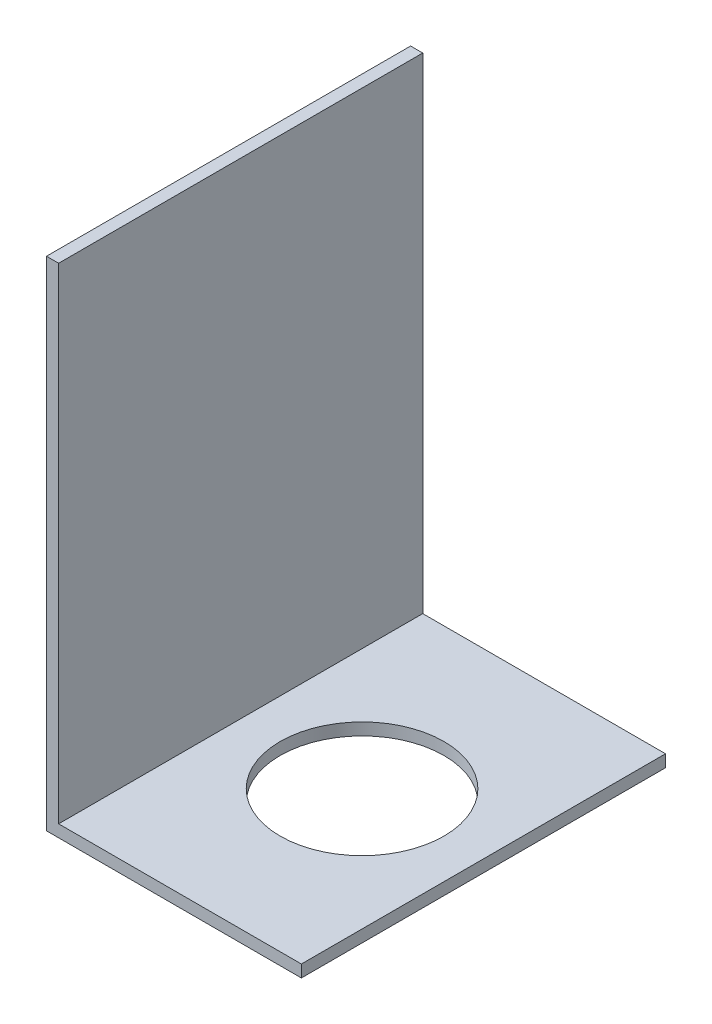
SolidWorks part; units mm, degrees
ref_plane "Front Plane" through (0, 0, 0) normal (0, 0, 1) x (1, 0, 0)
ref_plane "Top Plane" through (0, 0, 0) normal (0, 1, 0) x (1, 0, 0)
ref_plane "Right Plane" through (0, 0, 0) normal (1, 0, 0) x (0, 0, -1)
sketch "Sketch1" plane through (0, 0, 0) normal (0, 0, 1) x (1, 0, 0)
  line L0 (0, 40) -> (0, 0)
  line L1 (0, 0) -> (20, 0)
  dimension "D1" = 40
  dimension "D2" = 20
extrude "Extrude-Thin1" add sketch "Sketch1" along normal mid plane 30 thin
hole_wizard "M12 Clearance Slot1" positions "Sketch5" profile "Sketch4" size "M12" standard "ISO" slot yes end condition up to next
sketch "Sketch5" plane through (0, 0, 0) normal (0, 1, 0) x (1, 0, 0)
  line L0 (0, 15) -> (20, 15) construction
  line L2 (0, -15) -> (0, 15) construction
  point P0 (10, 0)
  dimension "D1" = 15
  dimension "D2" = 10
sketch "Sketch4" plane through (10, 0, 0) normal (1, 0, 0) x (0, 0, 1)
  line L0 (0, 0) -> (0, 1)
  line L1 (0, 1) -> (6.75, 1)
  line L2 (6.75, 1) -> (6.75, 0)
  line L5 (6.75, 0) -> (0, 0)
  line L11 (0, -6.35) -> (0, 107.95) construction
  dimension "Thru Hole Dia." = 13.5
  dimension "Thru Hole Depth" = 1
